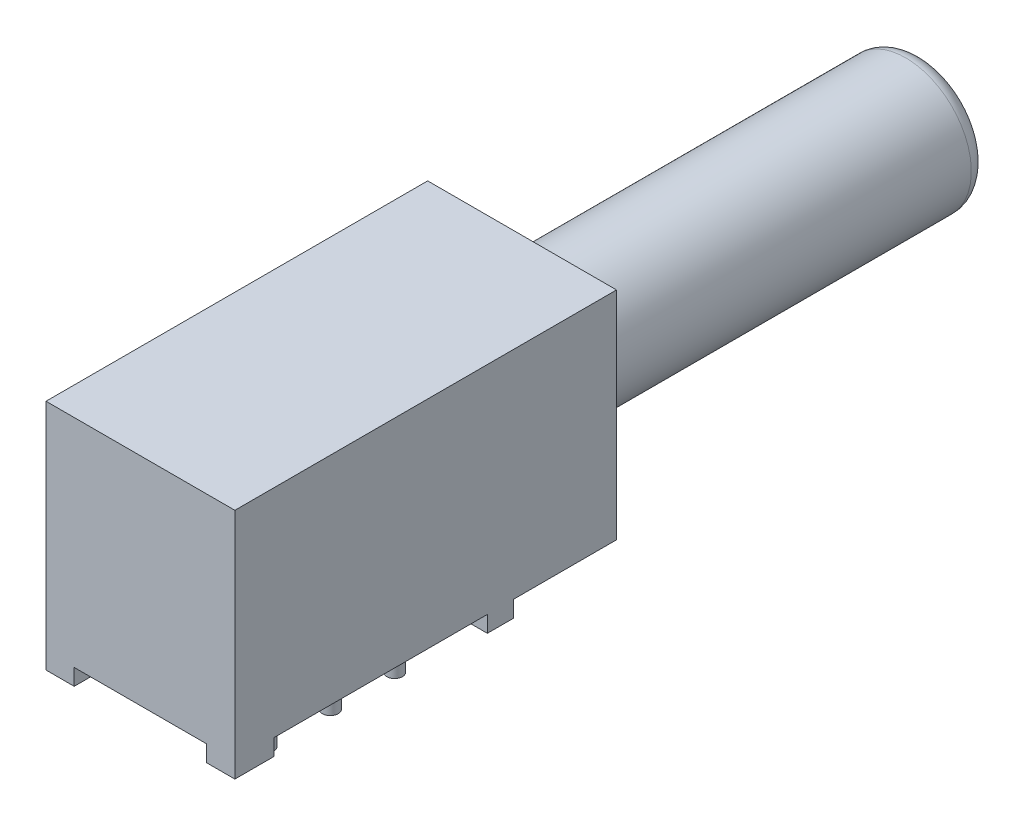
SolidWorks part; units mm, degrees
ref_plane "Front Plane" through (0, 0, 0) normal (0, 0, 1) x (1, 0, 0)
ref_plane "Top Plane" through (0, 0, 0) normal (0, 1, 0) x (1, 0, 0)
ref_plane "Right Plane" through (0, 0, 0) normal (1, 0, 0) x (0, 0, -1)
sketch "Sketch1" plane through (0, 0, 0) normal (0, 1, 0) x (1, 0, 0)
  circle A0 centre (0, 0) radius 0.3048
  circle A1 centre (0, -2.4892) radius 0.3048
  circle A2 centre (0, -4.9784) radius 0.3048
  circle A3 centre (2.5146, 0) radius 0.3048
  circle A4 centre (2.5146, -2.4892) radius 0.3048
  circle A5 centre (2.5146, -4.9784) radius 0.3048
  dimension "D1" = 2.5146
  dimension "D2" = 2.5146
  dimension "D3" = 2.5146
  dimension "D4" = 2.4892
  dimension "D5" = 2.4892
extrude "Pins" add sketch "Sketch1" against normal blind 2.54
sketch "Sketch2" plane through (0, 0, 0) normal (0, 1, 0) x (1, 0, 0)
  line L1 (-2.4003, -8.5852) -> (4.9149, -8.5852)
  line L3 (-2.4003, 2.2098) -> (4.9149, 2.2098)
  line L4 (4.9149, 2.2098) -> (4.9149, -8.5852)
  line L5 (-2.4003, 2.2098) -> (-2.4003, -8.5852)
  line L6 (-2.4003, 0.9182) -> (-2.4003, -10.9855) construction
  line L7 (0, -8.5852) -> (3.1643, -8.5852) construction
  line L8 (0, 0.9182) -> (0, -8.5852) construction
  line L9 (-2.4003, -10.9855) -> (3.1643, -10.9855) construction
  circle A0 centre (2.5146, 0) radius 0.3048 construction
  dimension "D3" = 2.4003
  dimension "D1" = 2.4003
  dimension "D2" = 8.5852
  dimension "D4" = 10.795
extrude "Main Body" add sketch "Sketch2" along normal blind 8.382
sketch "Sketch3" plane through (0, 0, 0) normal (0, -1, 0) x (1, 0, 0)
  line L0 (-2.4003, 8.5852) -> (4.9149, 8.5852) construction
  line L1 (-2.4003, -2.2098) -> (-2.4003, 8.5852) construction
  line L2 (4.9149, 8.5852) -> (4.9149, -2.2098) construction
  line L3 (4.9149, -2.2098) -> (-2.4003, -2.2098) construction
  line L4 (-2.4003, 8.5852) -> (4.9149, 8.5852)
  line L5 (-2.4003, -2.2098) -> (-2.4003, 8.5852)
  line L6 (4.9149, 8.5852) -> (4.9149, -2.2098)
  line L7 (4.9149, -2.2098) -> (-2.4003, -2.2098)
  line L8 (-2.4003, 7.0612) -> (-1.3081, 7.0612)
  line L9 (4.9149, -1.1938) -> (3.8227, -1.1938)
  line L10 (-1.3081, -2.2098) -> (-1.3081, -1.1938)
  line L11 (3.8227, 8.5852) -> (3.8227, 7.0612)
  line L12 (-1.3081, 7.0612) -> (-1.3081, 8.5852)
  line L13 (3.8227, 7.0612) -> (4.9149, 7.0612)
  line L14 (-1.3081, -2.2098) -> (-1.3081, 8.5852) construction
  line L15 (3.8227, -1.1938) -> (3.8227, -2.2098)
  line L16 (-2.4003, 7.0612) -> (4.9149, 7.0612) construction
  line L17 (-1.3081, -1.1938) -> (-2.4003, -1.1938)
  line L18 (3.8227, 8.5852) -> (3.8227, -2.2098) construction
  line L20 (4.9149, -1.1938) -> (-2.4003, -1.1938) construction
  line M7 (4.9149, -2.2098) -> (4.9149, 8.5852)
  line M8 (4.9149, 8.5852) -> (-2.4003, 8.5852)
  line M9 (-2.4003, 8.5852) -> (-2.4003, -2.2098)
  line M10 (-2.4003, -2.2098) -> (4.9149, -2.2098)
  dimension "D1" = 1.524
  dimension "D2" = 1.016
  dimension "D3" = 1.0922
  dimension "D4" = 1.0922
extrude "Feet" add sketch "Sketch3" along normal blind 0.635 contours L8 L12 M8 M9 | L11 L13 M7 M8 | L9 L15 M10 M7 | L10 L17 M9 M10
sketch "Sketch5" plane through (0, 0, -2.2098) normal (0, 0, -1) x (-1, 0, 0)
  line L0 (-4.9149, 8.382) -> (2.4003, 8.382) construction
  line L1 (-4.9149, 8.382) -> (2.4003, 8.382)
  line L2 (-4.9149, 8.382) -> (-4.9149, -0.635) construction
  line L3 (2.4003, 8.382) -> (2.4003, -0.635) construction
  line L4 (-4.9149, 8.382) -> (-4.9149, 0)
  line L5 (2.4003, 8.382) -> (2.4003, 0)
  line L6 (-4.9149, 0) -> (2.4003, 0)
extrude "Boss-Extrude5" add sketch "Sketch5" along normal blind 3.9878
sketch "Sketch4" plane through (0, 0, -2.2098) normal (0, 0, -1) x (-1, 0, 0)
  line L0 (2.4003, -0.635) -> (1.3081, -0.635) construction
  circle A0 centre (-1.2573, 4.3688) radius 2.54
  dimension "D1" = 5.0038
  dimension "D2" = 5.08
extrude "Cup" add sketch "Sketch4" along normal blind 19.4818
sketch "Sketch6" plane through (0, 0, -6.1976) normal (0, 0, -1) x (-1, 0, 0)
  circle A0 centre (-1.2573, 4.3688) radius 2.3495
extrude "Spring" add sketch "Sketch6" along normal blind 6.5532
fillet "Fillet1" radius 0.635 1 edges at (-1.2827, 4.3688, -21.6916)
